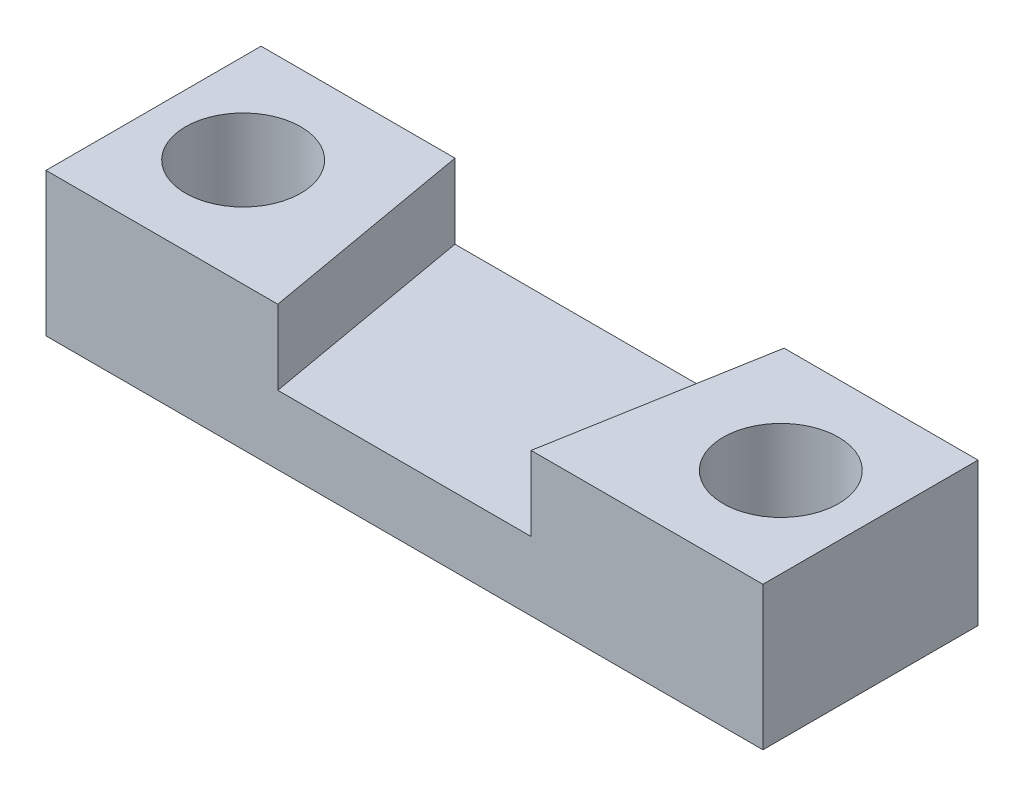
SolidWorks part; units mm, degrees
ref_plane "Front Plane" through (0, 0, 0) normal (0, 0, 1) x (1, 0, 0)
ref_plane "Top Plane" through (0, 0, 0) normal (0, 1, 0) x (1, 0, 0)
ref_plane "Right Plane" through (0, 0, 0) normal (1, 0, 0) x (0, 0, -1)
sketch "Sketch1" plane through (0, 0, 0) normal (0, 1, 0) x (1, 0, 0)
  line L1 (-15.875, -4.7625) -> (15.875, -4.7625)
  line L2 (-15.875, -4.7625) -> (-15.875, 4.7625)
  line L3 (-15.875, 4.7625) -> (15.875, 4.7625)
  line L4 (15.875, -4.7625) -> (15.875, 4.7625)
  point P4 (0, 4.7625)
  point P5 (-15.875, 0)
  dimension "D1" = 31.75
  dimension "D2" = 9.525
extrude "Boss-Extrude1" add sketch "Sketch1" along normal blind 6.35 contours L3 L4 L1 L2
hole_wizard "#10 Clearance Hole1" positions "Sketch2" profile "Sketch3" hole size "#10" standard "ANSI Inch"
sketch "Sketch2" plane through (0, 0, 0) normal (0, -1, 0) x (-1, 0, 0)
  point P0 (11.9062, 0)
  point P2 (-11.9062, 0)
  dimension "D1" = 23.8125
  dimension "D2" = 11.9062
sketch "Sketch3" plane through (-11.9062, 0, 0) normal (1, 0, 0) x (0, 0, -1)
  line L0 (0, 0) -> (0, 20.5838)
  line L1 (0, 20.5838) -> (2.5527, 19.05)
  line L2 (2.5527, 19.05) -> (2.5527, 0)
  line L5 (2.5527, 0) -> (0, 0)
  line L10 (0, 20.5838) -> (-2.5527, 19.05) construction
  line L11 (0, -6.35) -> (0, 107.95) construction
  dimension "Hole Dia." = 5.1054
  dimension "Hole Depth" = 19.05
  dimension "Drill Angle" = 118
sketch "Sketch4" plane through (0, 6.35, 0) normal (0, 1, 0) x (1, 0, 0)
  line L0 (7.2877, 4.7625) -> (5.6082, -4.7625)
  line L1 (-15.875, 4.7625) -> (15.875, 4.7625) construction
  line L2 (-15.875, -4.7625) -> (15.875, -4.7625) construction
  line L3 (-5.6082, -4.7625) -> (-7.2877, 4.7625)
  line L4 (-7.2877, 4.7625) -> (7.2877, 4.7625)
  line L6 (5.6082, -4.7625) -> (-5.6082, -4.7625)
  point P8 (6.4877, -4.7625)
  point P9 (4.3536, 4.7625)
  point P11 (8.0279, 4.7625)
  dimension "D1" = 80
  dimension "D2" = 6.35
  dimension "D3" = 80
  dimension "D4" = 6.35
extrude "Cut-Extrude1" cut sketch "Sketch4" against normal blind 3.302
equation "\"D2@Sketch2\"=\"D1@Sketch2\"/2"
equation "\"D1@Sketch4\"=\"D3@Sketch4\""
equation "\"D2@Sketch4\"=\"D4@Sketch4\""
